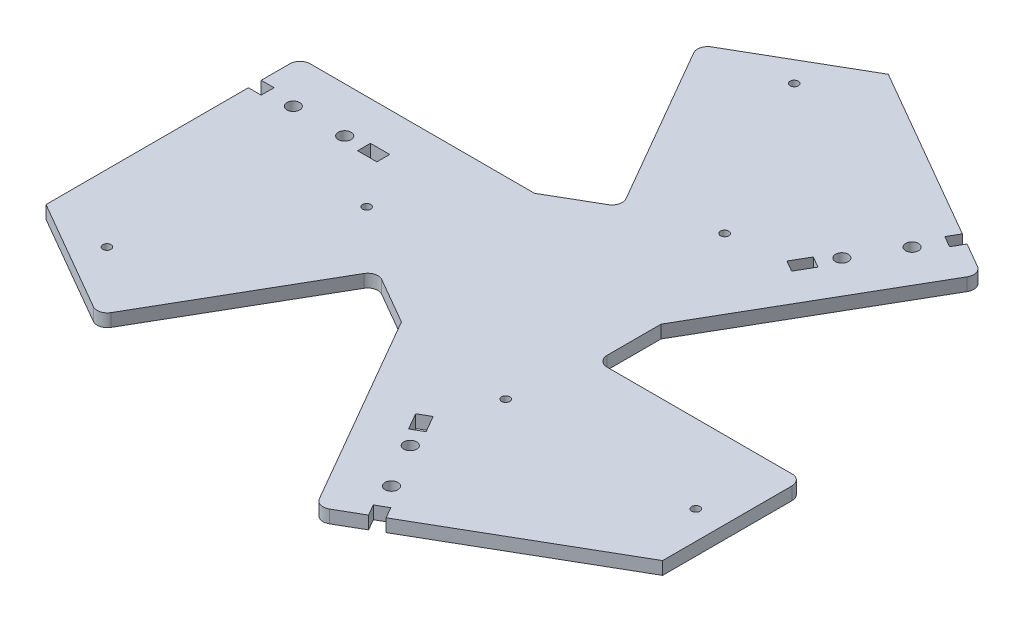
SolidWorks part; units mm, degrees
ref_plane "Front Plane" through (0, 0, 0) normal (0, 0, 1) x (1, 0, 0)
ref_plane "Top Plane" through (0, 0, 0) normal (0, 1, 0) x (1, 0, 0)
ref_plane "Right Plane" through (0, 0, 0) normal (1, 0, 0) x (0, 0, -1)
sketch "Sketch1" plane through (0, 0, 0) normal (0, 1, 0) x (1, 0, 0)
  line L0 (76.2, -43.9941) -> (76.2, 0) construction
  line L1 (76.2, -43.9941) -> (24.0219, -74.1191) construction
  line L2 (-18.2641, 18.7846) -> (-73.66, 18.7846)
  line L3 (-7.1556, -25.1981) -> (20.5522, -73.1894)
  line L4 (-76.2, -43.9941) -> (-76.2, 16.2446) construction
  line L5 (-76.2, -43.9941) -> (-38.1, -65.9911) construction
  line L6 (13.2563, -38.2006) -> (25013.2563, -43339.4708) construction
  line L7 (25.4, 6.4135) -> (25.4, -6.9215)
  line L8 (27.94, -9.4615) -> (73.66, -9.4615)
  line L9 (76.2, -12.0015) -> (76.2, -43.9941)
  line L10 (25.4, 6.4135) -> (53.0979, 54.3877)
  line L11 (-48.4936, -59.9904) -> (-76.2, -43.9941)
  line L12 (-22.1639, -19.466) -> (-45.0239, -59.0607)
  line L13 (-0.0099, 87.9825) -> (52.1682, 57.8574) construction
  line L14 (-7.1556, -25.1981) -> (-18.6942, -18.5363)
  line L15 (24.0219, -74.1191) -> (30.1261, -70.5949)
  line L16 (-0.0099, 87.9825) -> (-38.1, 65.9911) construction
  line L17 (-27.7064, 71.9919) -> (-0.0099, 87.9825)
  line L18 (-5.7761, 28.9275) -> (-28.6361, 68.5222)
  line L19 (30.1261, -70.5949) -> (28.5386, -67.8453)
  line L20 (-18.2641, 18.7846) -> (-6.7058, 25.4578)
  line L21 (0, 0) -> (-49999.9986, 0) construction
  line L22 (0, 0) -> (-25000, 43301.2702) construction
  line L23 (0, 0) -> (-25000, -43301.2702) construction
  line L24 (25.4, 0) -> (76.2, 0) construction
  line L25 (-12.7, -21.997) -> (-38.1, -65.9911) construction
  line L26 (-12.7, 21.997) -> (-38.1, 65.9911) construction
  line L27 (76.2, 8.001) -> (76.2, 45.974) [skipped]
  line L28 (-31.1709, -69.9916) -> (1.7147, -88.9781) [skipped]
  line L29 (-45.0291, 61.9906) -> (-77.9147, 43.0041) [skipped]
  line L30 (-32.5457, -69.1979) -> (-7.1457, -25.2038) [skipped]
  line L31 (-43.6543, 62.7844) -> (-18.2543, 18.7903) [skipped]
  line L32 (76.2, 6.4135) -> (25.4, 6.4135) [skipped]
  line L33 (28.5386, -67.8453) -> (31.2882, -66.2578)
  line L34 (31.2882, -66.2578) -> (32.8757, -69.0074)
  line L35 (32.8757, -69.0074) -> (76.2, -43.9941)
  line L36 (-53.975, 7.6086) -> (-66.675, 7.6086) construction
  line L37 (33.5767, 42.928) -> (39.9267, 53.9265) construction
  line L38 (-0.0099, 87.9825) -> (43.3144, 62.9692)
  line L39 (-73.025, 9.1961) -> (-73.025, 6.0211)
  line L40 (46.064, 61.3817) -> (52.1682, 57.8574)
  line L41 (-73.025, 6.0211) -> (-76.2, 6.0211)
  line L42 (-76.2, 9.1961) -> (-73.025, 9.1961)
  line L43 (-76.2, 16.2446) -> (-76.2, 9.1961)
  line L44 (44.4765, 58.6321) -> (41.7269, 60.2196)
  line L45 (-76.2, 6.0211) -> (-76.2, -43.9941)
  line L46 (41.7269, 60.2196) -> (43.3144, 62.9692)
  line L47 (46.064, 61.3817) -> (44.4765, 58.6321)
  line L48 (-76.2, 6.0211) -> (-76.2, -44.0055) [skipped]
  line L49 (-76.2, 16.2446) -> (-76.2, 9.1961) [skipped]
  line L50 (43.3144, 62.9692) -> (-0.0099, 87.9825) [skipped]
  line L51 (52.1682, 57.8574) -> (46.064, 61.3817) [skipped]
  line L52 (14.2511, -43.0986) -> (16.6323, -47.223)
  line L53 (16.6323, -47.223) -> (19.382, -45.6355)
  line L54 (19.382, -45.6355) -> (17.0007, -41.5111)
  line L55 (17.0007, -41.5111) -> (14.2511, -43.0986)
  line L56 (-49.2125, 6.0325) -> (-44.45, 6.0325)
  line L57 (-49.2125, 9.2075) -> (-49.2125, 6.0325)
  line L58 (-44.45, 9.2075) -> (-49.2125, 9.2075)
  line L59 (-44.45, 6.0325) -> (-44.45, 9.2075)
  line L60 (29.8305, 39.603) -> (27.4493, 35.4786)
  line L61 (32.5802, 38.0155) -> (29.8305, 39.603)
  line L62 (30.1989, 33.8911) -> (32.5802, 38.0155)
  line L63 (27.4493, 35.4786) -> (30.1989, 33.8911)
  circle A0 centre (69.2404, -28.829) radius 1.016
  circle A1 centre (0, 0) radius 76.2 construction
  circle A2 centre (-59.5868, -45.5494) radius 1.016
  circle A3 centre (-9.6536, 74.3784) radius 1.016
  circle A4 centre (22.2504, -28.829) radius 1.016
  circle A5 centre (-36.0918, -4.8549) radius 1.016
  circle A6 centre (13.8414, 33.6839) radius 1.016
  circle A7 centre (26.7384, -61.5522) radius 1.5875
  circle A8 centre (20.3884, -50.5537) radius 1.5875
  circle A9 centre (-53.975, 7.6086) radius 1.5875
  circle A10 centre (-66.675, 7.6086) radius 1.5875
  circle A11 centre (33.5767, 42.928) radius 1.5875
  circle A12 centre (39.9267, 53.9265) radius 1.5875
  arc A13 (24.0219, -74.1191) -> (20.5522, -73.1894) centre (22.7519, -71.9194) cw
  arc A14 (73.66, -9.4615) -> (76.2, -12.0015) centre (73.66, -12.0015) cw
  arc A15 (53.0979, 54.3877) -> (52.1682, 57.8574) centre (50.8982, 55.6577) ccw
  arc A16 (-27.7064, 71.9919) -> (-28.6361, 68.5222) centre (-26.4364, 69.7922) ccw
  arc A17 (-48.4936, -59.9904) -> (-45.0239, -59.0607) centre (-47.2236, -57.7907) ccw
  arc A18 (-73.66, 18.7846) -> (-76.2, 16.2446) centre (-73.66, 16.2446) ccw
  arc A19 (-22.1639, -19.466) -> (-18.6942, -18.5363) centre (-19.9642, -20.736) cw
  arc A20 (25.4, -6.9215) -> (27.94, -9.4615) centre (27.94, -6.9215) ccw
  arc A21 (-5.7761, 28.9275) -> (-6.7058, 25.4578) centre (-7.9758, 27.6575) cw
  point P72 (76.2, -9.4615)
  point P85 (25.4, -9.4615)
  point P88 (29.9134, -67.0515)
  point P97 (15.6259, -42.3048)
  dimension "D2" = 15.875
  dimension "D6" = 152.4
  dimension "D13" = 2.032
  dimension "D17" = 2.032
  dimension "D21" = 3.175
  dimension "D22" = 3.175
  dimension "D25" = 2.54
  dimension "D1" = 120
  dimension "D3" = 50.8
  dimension "D4" = 3
  dimension "D5" = 3
  dimension "D7" = 9.4615
  dimension "D9" = 120
  dimension "D10" = 120
  dimension "D11" = 6.9596
  dimension "D12" = 19.3675
  dimension "D15" = 19.3675
  dimension "D16" = 53.9496
  dimension "D19" = 9.525
  dimension "D20" = 12.7
  dimension "D24" = 7.62
  dimension "D26" = 3.175
  dimension "D27" = 3.175
  dimension "D28" = 11.176
  dimension "D29" = 11.176
  dimension "D30" = 11.176
  dimension "D31" = 6.9596
  dimension "D32" = 19.3675
  dimension "D33" = 19.3675
  dimension "D34" = 53.9496
  dimension "D36" = 4.7625
  dimension "D37" = 9.525
  dimension "D38" = 3.175
  dimension "D8" = 3
  dimension "D14" = 3
  dimension "D18" = 3
  dimension "D23" = 3
  dimension "D35" = 3
  dimension "D39" = 3
extrude "Boss-Extrude2" add sketch "Sketch1" along normal blind 3.175
